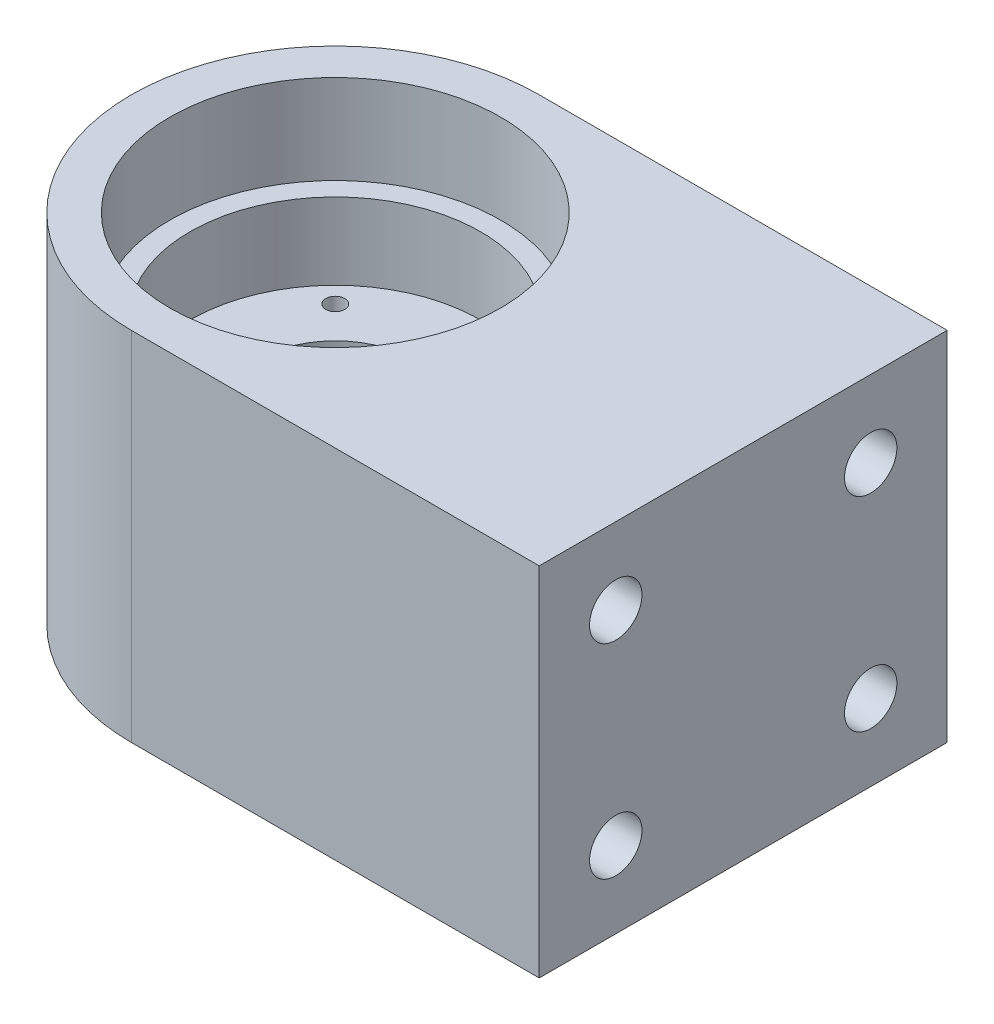
SolidWorks part; units mm, degrees
material "6061-T6 (SS)"
ref_plane "Front Plane" through (0, 0, 0) normal (0, 0, 1) x (1, 0, 0)
ref_plane "Top Plane" through (0, 0, 0) normal (0, 1, 0) x (1, 0, 0)
ref_plane "Right Plane" through (0, 0, 0) normal (1, 0, 0) x (0, 0, -1)
sketch "Sketch1" plane through (0, 0, 0) normal (0, 1, 0) x (1, 0, 0)
  line L0 (-25.4, 25.4) -> (-25.4, -25.4)
  line L1 (-25.4, -25.4) -> (50.8, -25.4)
  line L2 (50.8, -25.4) -> (50.8, 25.4)
  line L3 (50.8, 25.4) -> (-25.4, 25.4)
  line L4 (-20.955, 0) -> (20.955, 0) construction
  line L5 (0, -20.955) -> (0, 20.955) construction
  dimension "D1" = 25.4
  dimension "D2" = 50.8
  dimension "D3" = 76.2
  dimension "D4" = 25.4
extrude "Boss-Extrude1" add sketch "Sketch1" along normal mid plane 44.45
sketch "Sketch2" plane through (0, 22.225, 0) normal (0, 1, 0) x (1, 0, 0)
  circle A0 centre (0, 0) radius 20.5994
  dimension "D1" = 41.1988
extrude "Cut-Extrude1" cut sketch "Sketch2" against normal blind 11.1125
sketch "Sketch3" plane through (0, 11.1125, 0) normal (0, 1, 0) x (1, 0, 0)
  circle A0 centre (0, 0) radius 18.0975
  dimension "D1" = 36.195
extrude "Cut-Extrude2" cut sketch "Sketch3" against normal blind 9.525
sketch "Sketch4" plane through (0, 1.5875, 0) normal (0, 1, 0) x (1, 0, 0)
  circle A0 centre (0, 0) radius 9.6266
  dimension "D1" = 19.2532
extrude "Cut-Extrude3" cut sketch "Sketch4" against normal through all
sketch "Sketch5" plane through (0, -22.225, 0) normal (0, -1, 0) x (1, 0, 0)
  circle A0 centre (0, 0) radius 19.05
  dimension "D1" = 38.1
extrude "Cut-Extrude4" cut sketch "Sketch5" against normal offset from surface (17.4625 mm away) 6.35 up to face at (0, 1.5875, 9.6266)
sketch "Sketch6" plane through (0, -4.7625, 0) normal (0, -1, 0) x (1, 0, 0)
  circle A0 centre (0, 0) radius 11.303
  dimension "D1" = 22.606
extrude "Cut-Extrude5" cut sketch "Sketch6" against normal blind 1.397
sketch "Sketch7" plane through (50.8, 0, 0) normal (1, 0, 0) x (0, 0, -1)
  line L0 (-25.4, 22.225) -> (-25.4, -22.225) construction
  line L1 (15.875, -12.7) -> (-15.875, -12.7) construction
  line L2 (15.875, -12.7) -> (15.875, 12.7) construction
  line L3 (15.875, 12.7) -> (-15.875, 12.7) construction
  line L4 (-15.875, -12.7) -> (-15.875, 12.7) construction
  line L5 (15.875, -12.7) -> (-15.875, 12.7) construction
  line L6 (15.875, 12.7) -> (-15.875, -12.7) construction
  line L7 (-25.4, 22.225) -> (25.4, 22.225) construction
  circle A0 centre (-15.875, 12.7) radius 3.2639
  circle A1 centre (15.875, 12.7) radius 3.2639
  circle A2 centre (-15.875, -12.7) radius 3.2639
  circle A3 centre (15.875, -12.7) radius 3.2639
  point P0 (0, 0)
  dimension "D3" = 6.5278
  dimension "D1" = 9.525
  dimension "D2" = 9.525
extrude "Cut-Extrude6" cut sketch "Sketch7" against normal blind 19.05
sketch "Sketch8" plane through (0, -4.7625, 0) normal (0, -1, 0) x (1, 0, 0)
  line L0 (0, 0) -> (-10.7763, 10.7763) construction
  line L1 (24.4475, 0) -> (-24.4475, 0) construction
  circle A0 centre (0, 0) radius 15.24 construction
  circle A1 centre (-10.7763, 10.7763) radius 1.1811
  dimension "D1" = 30.48
  dimension "D3" = 2.3622
  dimension "D2" = 45
extrude "Cut-Extrude7" cut sketch "Sketch8" against normal through all
pattern_circular "CirPattern1" count 4 over 360 about axis through (0, 0, 0) along (0, 1, 0) of "Cut-Extrude7"
sketch "Sketch9" plane through (0, -22.225, 0) normal (0, -1, 0) x (1, 0, 0)
  line L0 (50.8, -25.4) -> (-25.4, -25.4) construction
  line L1 (0, 25.4) -> (0, 38.1)
  line L2 (0, 38.1) -> (-38.1, 38.1)
  line L3 (-38.1, 38.1) -> (-38.1, -38.1)
  line L4 (-38.1, -38.1) -> (0, -38.1)
  line L5 (0, -38.1) -> (0, -25.4)
  line L6 (-25.4, 25.4) -> (50.8, 25.4) construction
  arc A1 (0, -25.4) -> (0, 25.4) centre (0, 0) cw
  point P0 (0, -25.4)
  dimension "D1" = 76.2
  dimension "D2" = 12.7
  dimension "D3" = 38.1
extrude "Cut-Extrude8" cut sketch "Sketch9" against normal through all
